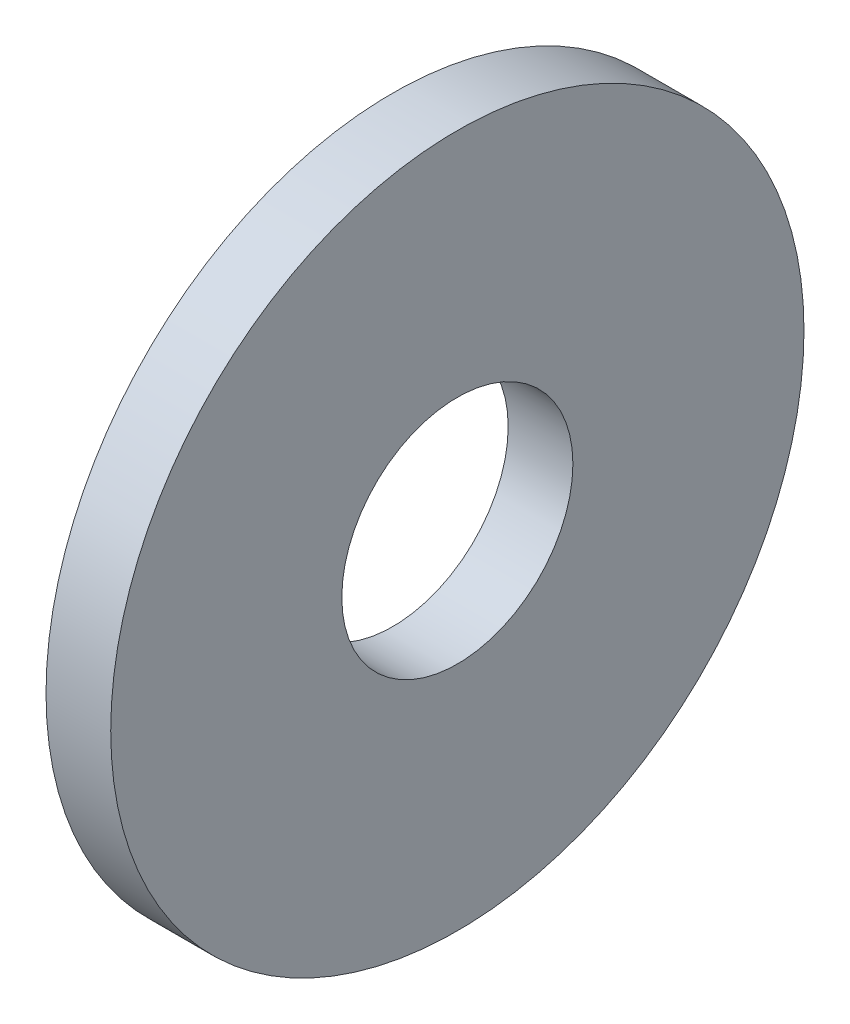
SolidWorks part; units mm, degrees
ref_plane "Front Plane" through (0, 0, 0) normal (0, 0, 1) x (1, 0, 0)
ref_plane "Top Plane" through (0, 0, 0) normal (0, 1, 0) x (1, 0, 0)
ref_plane "Right Plane" through (0, 0, 0) normal (1, 0, 0) x (0, 0, -1)
sketch "Sketch1" plane through (0, 0, 0) normal (1, 0, 0) x (0, 0, -1)
  circle A0 centre (0, 0) radius 19.05
  circle A1 centre (0, 0) radius 6.35
  dimension "OD" = 38.1
  dimension "ID" = 12.7
extrude "Boss-Extrude1" add sketch "Sketch1" along normal blind 3.556
